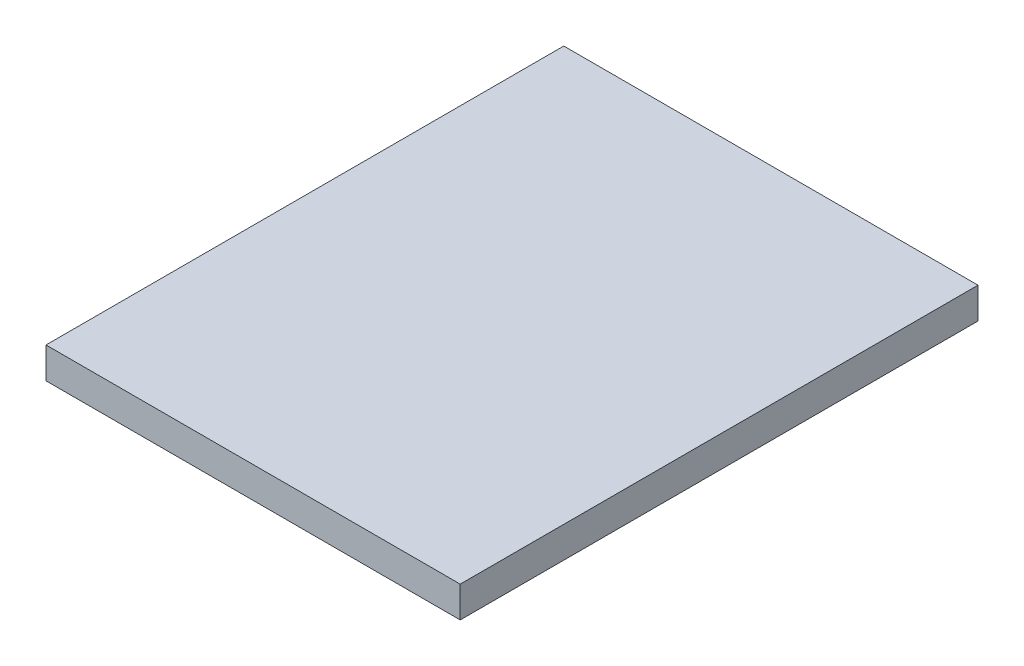
SolidWorks part; units mm, degrees
ref_plane "Front Plane" through (0, 0, 0) normal (0, 0, 1) x (1, 0, 0)
ref_plane "Top Plane" through (0, 0, 0) normal (0, 1, 0) x (1, 0, 0)
ref_plane "Right Plane" through (0, 0, 0) normal (1, 0, 0) x (0, 0, -1)
sketch "Sketch1" plane through (0, 0, 0) normal (0, 1, 0) x (1, 0, 0)
  line L1 (0, 0) -> (80, 0)
  line L2 (0, 0) -> (0, 100)
  line L3 (0, 100) -> (80, 100)
  line L4 (80, 0) -> (80, 100)
  dimension "D1" = 100
  dimension "D2" = 80
sketch "Sketch2" plane through (0, 0, 0) normal (0, 1, 0) x (1, 0, 0)
  line L0 (0, 0) -> (80, 0)
  line L1 (0, 0) -> (0, 100)
  line L2 (0, 100) -> (80, 100)
  line L3 (80, 0) -> (80, 100)
extrude "Boss-Extrude1" add sketch "Sketch2" along normal blind 6
scale "Scale1" scale about centroid uniform scaling yes scale factor 7.5
